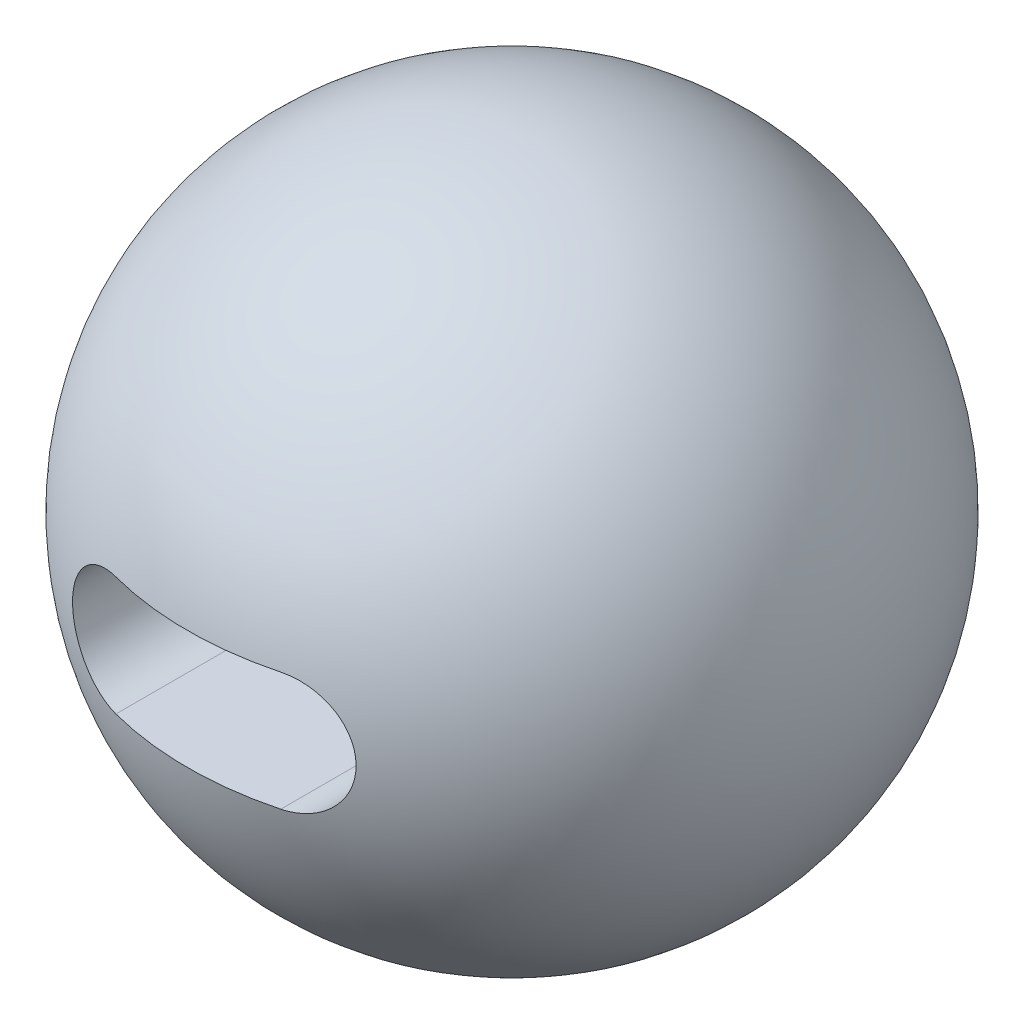
SolidWorks part; units mm, degrees
material "AISI 304"
ref_plane "Front Plane" through (0, 0, 0) normal (0, 0, 1) x (1, 0, 0)
ref_plane "Top Plane" through (0, 0, 0) normal (0, 1, 0) x (1, 0, 0)
ref_plane "Right Plane" through (0, 0, 0) normal (1, 0, 0) x (0, 0, -1)
sketch "Sketch1" plane through (0, 0, 0) normal (0, 0, 1) x (1, 0, 0)
  line L0 (0, -500) -> (0, 500)
  arc A0 (0, 500) -> (0, -500) centre (0, 0) ccw
  point P6 (0, 0)
  dimension "D1" = 1000
revolve "Revolve1" add sketch "Sketch1" angle 360 about L0
ref_plane "Plane2" through (0, 0, 500) normal (0, 0, 1) x (1, 0, 0)
sketch "Sketch7" plane through (0, 0, 500) normal (0, 0, 1) x (1, 0, 0)
  line L0 (-125, 0) -> (125, 0) construction
  line L1 (-125, 90) -> (125, 90)
  line L2 (-125, -90) -> (125, -90)
  arc A0 (-125, 90) -> (-125, -90) centre (-125, 0) ccw
  arc A1 (125, -90) -> (125, 90) centre (125, 0) ccw
  point P3 (0, 0)
  dimension "D2" = 90
  dimension "D1" = 250
extrude "Cut-Extrude2" cut sketch "Sketch7" against normal blind 500
